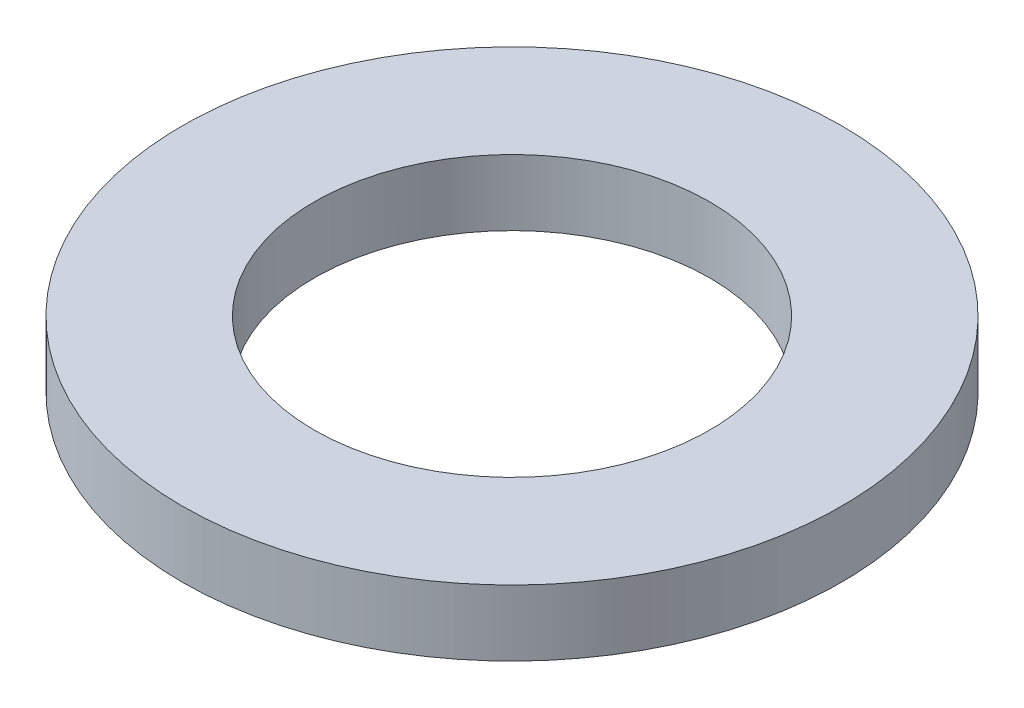
SolidWorks part; units mm, degrees
ref_plane "前视基准面" through (0, 0, 0) normal (0, 0, 1) x (1, 0, 0)
ref_plane "上视基准面" through (0, 0, 0) normal (0, 1, 0) x (1, 0, 0)
ref_plane "右视基准面" through (0, 0, 0) normal (1, 0, 0) x (0, 0, -1)
sketch "草图1" plane through (0, 0, 0) normal (0, 1, 0) x (1, 0, 0)
  circle A0 centre (0, 0) radius 15
  dimension "D1" = 30
extrude "凸台-拉伸1" add sketch "草图1" along normal blind 3
sketch "草图2" plane through (0, 0, 0) normal (0, -1, 0) x (1, 0, 0)
  circle A0 centre (0, 0) radius 9
  dimension "D1" = 18
extrude "切除-拉伸1" cut sketch "草图2" against normal blind 24.5
